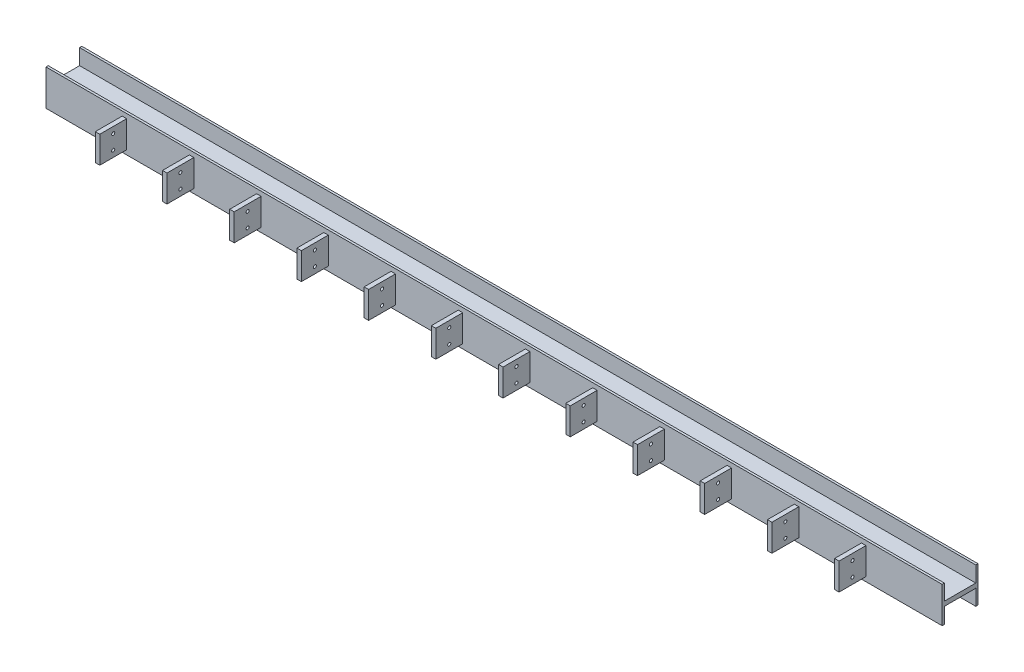
SolidWorks part; units mm, degrees
ref_plane "Front Plane" through (0, 0, 0) normal (0, 0, 1) x (1, 0, 0)
ref_plane "Top Plane" through (0, 0, 0) normal (0, 1, 0) x (1, 0, 0)
ref_plane "Right Plane" through (0, 0, 0) normal (1, 0, 0) x (0, 0, -1)
sketch "Sketch1" plane through (0, 0, 0) normal (0, 0, 1) x (1, 0, 0)
  line L1 (-5000, -200) -> (5000, -200)
  line L2 (-5000, -200) -> (-5000, 200)
  line L3 (-5000, 200) -> (5000, 200)
  line L4 (5000, -200) -> (5000, 200)
  line L5 (-5000, -200) -> (5000, 200) construction
  line L6 (-5000, 200) -> (5000, -200) construction
  point P0 (0, 0)
  dimension "D1" = 10000
  dimension "D2" = 400
extrude "Boss-Extrude1" add sketch "Sketch1" along normal blind 400
sketch "Sketch2" plane through (5000, 0, 0) normal (1, 0, 0) x (0, 0, -1)
  line L0 (-400, 200) -> (0, 200) construction
  line L1 (-375, 200) -> (-25, 200)
  line L2 (-375, 200) -> (-375, 25)
  line L3 (-375, 25) -> (-25, 25)
  line L4 (-25, 200) -> (-25, 25)
  line L5 (0, 0) -> (-400, 0) construction
  line L6 (-400, -200) -> (-400, 200) construction
  line L7 (0, -200) -> (0, 200) construction
  line L8 (-25, -200) -> (-25, -25)
  line L9 (-375, -25) -> (-25, -25)
  line L10 (-375, -200) -> (-375, -25)
  line L11 (-375, -200) -> (-25, -200)
  dimension "D1" = 25
  dimension "D2" = 25
  dimension "D3" = 25
extrude "Cut-Extrude1" cut sketch "Sketch2" against normal blind 10100
sketch "Sketch3" plane through (0, 0, 400) normal (0, 0, 1) x (1, 0, 0)
  line L3 (-5000, 0) -> (5000, 0) construction
  line L142 (-5000, 200) -> (-5000, -200) construction
  line L145 (5000, -200) -> (5000, 200) construction
  line L146 (0, 200) -> (0, -200) construction
  line L148 (5000, 200) -> (-5000, 200) construction
  line L149 (-5000, -200) -> (5000, -200) construction
  line L150 (-3350, -150) -> (-3350, 150)
  line L151 (-4150, -150) -> (-4100, -150)
  line L152 (-4150, -150) -> (-4150, 150)
  line L153 (-4150, 150) -> (-4100, 150)
  line L154 (-4100, -150) -> (-4100, 150)
  line L155 (-4150, -150) -> (-4100, 150) construction
  line L156 (-4150, 150) -> (-4100, -150) construction
  line L157 (-3400, -150) -> (-3400, 150)
  line L158 (-3400, 150) -> (-3350, 150)
  line L159 (-3400, -150) -> (-3350, -150)
  line L160 (-2600, -150) -> (-2600, 150)
  line L161 (-2650, -150) -> (-2650, 150)
  line L162 (-2650, 150) -> (-2600, 150)
  line L163 (-2650, -150) -> (-2600, -150)
  line L164 (-1850, -150) -> (-1850, 150)
  line L165 (-1900, -150) -> (-1900, 150)
  line L166 (-1900, 150) -> (-1850, 150)
  line L167 (-1900, -150) -> (-1850, -150)
  line L168 (-1100, -150) -> (-1100, 150)
  line L169 (-1150, -150) -> (-1150, 150)
  line L170 (-1150, 150) -> (-1100, 150)
  line L171 (-1150, -150) -> (-1100, -150)
  line L172 (-350, -150) -> (-350, 150)
  line L173 (-400, -150) -> (-400, 150)
  line L174 (-400, 150) -> (-350, 150)
  line L175 (-400, -150) -> (-350, -150)
  line L176 (400, -150) -> (400, 150)
  line L177 (350, -150) -> (350, 150)
  line L178 (350, 150) -> (400, 150)
  line L179 (350, -150) -> (400, -150)
  line L180 (1150, -150) -> (1150, 150)
  line L181 (1100, -150) -> (1100, 150)
  line L182 (1100, 150) -> (1150, 150)
  line L183 (1100, -150) -> (1150, -150)
  line L184 (1900, -150) -> (1900, 150)
  line L185 (1850, -150) -> (1850, 150)
  line L186 (1850, 150) -> (1900, 150)
  line L187 (1850, -150) -> (1900, -150)
  line L188 (2650, -150) -> (2650, 150)
  line L189 (2600, -150) -> (2600, 150)
  line L190 (2600, 150) -> (2650, 150)
  line L191 (2600, -150) -> (2650, -150)
  line L192 (3400, -150) -> (3400, 150)
  line L193 (3350, -150) -> (3350, 150)
  line L194 (3350, 150) -> (3400, 150)
  line L195 (3350, -150) -> (3400, -150)
  line L196 (4150, -150) -> (4150, 150)
  line L197 (4100, -150) -> (4100, 150)
  line L198 (4100, 150) -> (4150, 150)
  line L199 (4100, -150) -> (4150, -150)
  point P12 (-4125, 0)
  dimension "D1" = 50
  dimension "D2" = 300
  dimension "D4" = 700
  dimension "D5" = 350
  dimension "D3" = 12
extrude "Boss-Extrude2" add sketch "Sketch3" along normal blind 300
sketch "Sketch4" plane through (4150, 0, 0) normal (1, 0, 0) x (0, 0, -1)
  line L0 (-550, 150) -> (-550, -150) construction
  line L1 (-700, 150) -> (-400, 150) construction
  line L2 (-700, -150) -> (-400, -150) construction
  line L3 (-550, 0) -> (-700, 0) construction
  line L4 (-700, -150) -> (-700, 150) construction
  circle A0 centre (-550, 80) radius 17.5
  circle A1 centre (-550, -80) radius 17.5
  dimension "D1" = 35
  dimension "D2" = 70
extrude "Cut-Extrude2" cut sketch "Sketch4" against normal blind 8530
